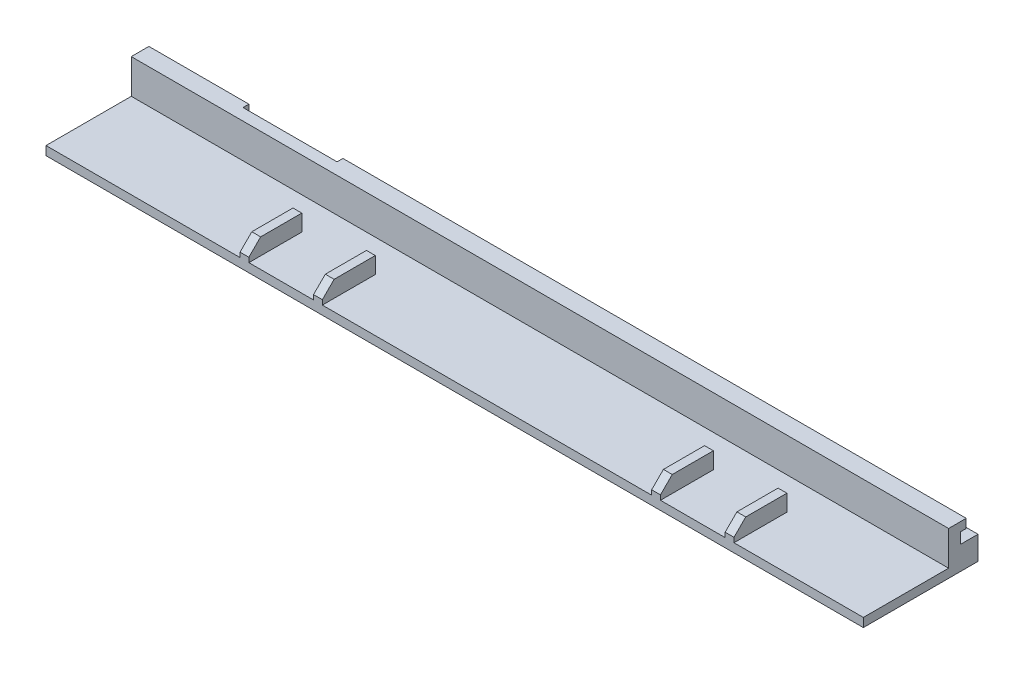
SolidWorks part; units mm, degrees
ref_plane "Front Plane" through (0, 0, 0) normal (0, 0, 1) x (1, 0, 0)
ref_plane "Top Plane" through (0, 0, 0) normal (0, 1, 0) x (1, 0, 0)
ref_plane "Right Plane" through (0, 0, 0) normal (1, 0, 0) x (0, 0, -1)
sketch "Sketch1" plane through (0, 0, 0) normal (1, 0, 0) x (0, 0, -1)
  line L0 (0, 0) -> (-16.5, 0)
  line L1 (-16.5, 0) -> (-16.5, 1.5)
  line L2 (-16.5, 1.5) -> (-2, 1.5)
  line L3 (0, 0) -> (0, 9.5667) construction
  line L4 (0, 0) -> (3, 0)
  line L5 (3, 0) -> (3, 4)
  line L6 (3, 4) -> (0, 4)
  line L7 (-2, 4) -> (-2, 1.5)
  line L8 (0, 4) -> (0, 5.85)
  line L9 (0, 5.85) -> (1, 5.85)
  line L10 (1, 5.85) -> (1, 7.35)
  line L11 (1, 7.35) -> (-2, 7.35)
  line L12 (-2, 4) -> (-2, 7.35)
  dimension "D1" = 16.5
  dimension "D2" = 3
  dimension "D3" = 4
  dimension "D4" = 2
  dimension "D5" = 1.5
  dimension "D6" = 1.85
  dimension "D7" = 1.5
  dimension "D8" = 3
extrude "Boss-Extrude1" add sketch "Sketch1" along normal blind 150
sketch "Sketch2" plane through (0, 1.5, 0) normal (0, 1, 0) x (1, 0, 0)
  line L0 (40, -2) -> (40, -16.5) construction
  line L1 (150, -2) -> (0, -2) construction
  line L2 (150, -16.5) -> (0, -16.5) construction
  line L3 (110, -2) -> (110, -16.5) construction
  line L5 (75, -16.5) -> (75, -2) construction
  line L6 (33, -16.5) -> (34.5, -16.5)
  line L7 (33, -16.5) -> (33, -7.5)
  line L8 (33, -7.5) -> (34.5, -7.5)
  line L9 (34.5, -16.5) -> (34.5, -7.5)
  line L10 (45.5, -16.5) -> (47, -16.5)
  line L11 (45.5, -16.5) -> (45.5, -7.5)
  line L12 (45.5, -7.5) -> (47, -7.5)
  line L13 (47, -16.5) -> (47, -7.5)
  line L14 (103, -16.5) -> (104.5, -16.5)
  line L15 (103, -16.5) -> (103, -7.5)
  line L16 (103, -7.5) -> (104.5, -7.5)
  line L17 (104.5, -16.5) -> (104.5, -7.5)
  line L18 (115.5, -16.5) -> (117, -16.5)
  line L19 (115.5, -16.5) -> (115.5, -7.5)
  line L20 (115.5, -7.5) -> (117, -7.5)
  line L21 (117, -16.5) -> (117, -7.5)
  point P8 (110, -9.25)
  dimension "D1" = 35
  dimension "D2" = 35
  dimension "D3" = 9
  dimension "D4" = 1.5
  dimension "D5" = 11
  dimension "D6" = 11
extrude "Boss-Extrude2" add sketch "Sketch2" along normal blind 2.8
sketch "Sketch4" plane through (0, 7.35, 0) normal (0, 1, 0) x (1, 0, 0)
  line L2 (150, 3) -> (0, 3) construction
  line L3 (33, 0) -> (17, 0)
  line L4 (33, 0) -> (33, 3)
  line L5 (33, 3) -> (17, 3)
  line L6 (17, 0) -> (17, 3)
  line L7 (33, -7.5) -> (33, -16.5) construction
  line L8 (150, -16.5) -> (117, -16.5) construction
  line L9 (150, 3) -> (139, 3)
  line L10 (150, 3) -> (150, -16.5)
  line L11 (150, -16.5) -> (139, -16.5)
  line L12 (139, 3) -> (139, -16.5)
  line L13 (117, -16.5) -> (117, -7.5) construction
  dimension "D1" = 16
  dimension "D2" = 22
extrude "Cut-Extrude2" cut sketch "Sketch4" against normal blind 22
chamfer "Chamfer1" distance 2 angle 45 4 edges at (116.25, 4.3, 16.5) (103.75, 4.3, 16.5) (46.25, 4.3, 16.5) (33.75, 4.3, 16.5)
